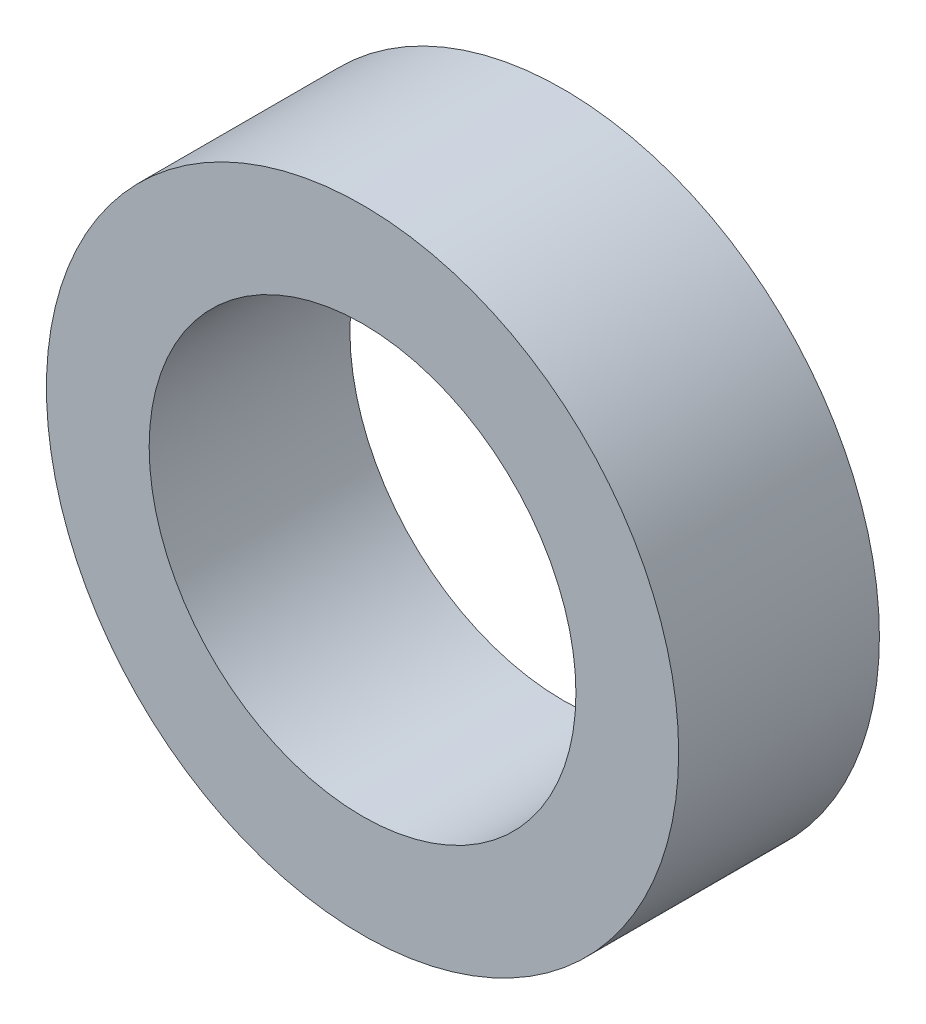
SolidWorks part; units mm, degrees
ref_plane "Front Plane" through (0, 0, 0) normal (0, 0, 1) x (1, 0, 0)
ref_plane "Top Plane" through (0, 0, 0) normal (0, 1, 0) x (1, 0, 0)
ref_plane "Right Plane" through (0, 0, 0) normal (1, 0, 0) x (0, 0, -1)
sketch "Sketch1" plane through (0, 0, 0) normal (0, 0, 1) x (1, 0, 0)
  circle A0 centre (0, 0) radius 4
  circle A1 centre (0, 0) radius 2.7
  point P4 (0, 0)
extrude "Boss-Extrude2" add sketch "Sketch1" along normal blind 2.54
